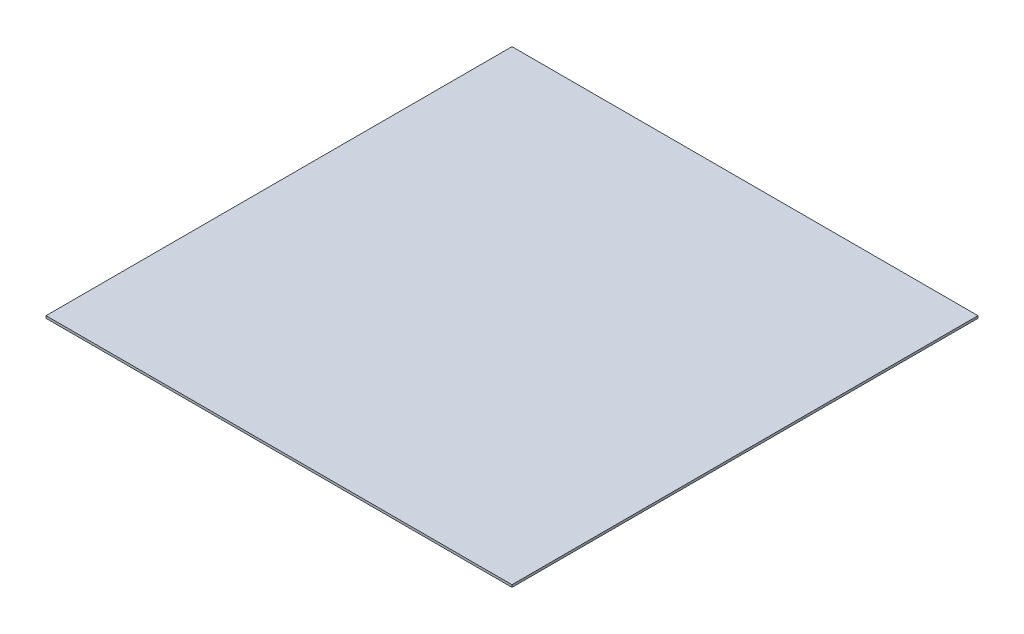
SolidWorks part; units mm, degrees
ref_plane "Front Plane" through (0, 0, 0) normal (0, 0, 1) x (1, 0, 0)
ref_plane "Top Plane" through (0, 0, 0) normal (0, 1, 0) x (1, 0, 0)
ref_plane "Right Plane" through (0, 0, 0) normal (1, 0, 0) x (0, 0, -1)
sketch "Sketch1" plane through (0, 0, 0) normal (0, 1, 0) x (1, 0, 0)
  line L1 (50, 50) -> (-50, 50)
  line L2 (50, 50) -> (50, -50)
  line L3 (50, -50) -> (-50, -50)
  line L4 (-50, 50) -> (-50, -50)
  line L5 (50, 50) -> (-50, -50) construction
  line L6 (50, -50) -> (-50, 50) construction
  point P0 (0, 0)
  dimension "D1" = 100
  dimension "D2" = 100
extrude "Boss-Extrude1" add sketch "Sketch1" along normal blind 0.5
